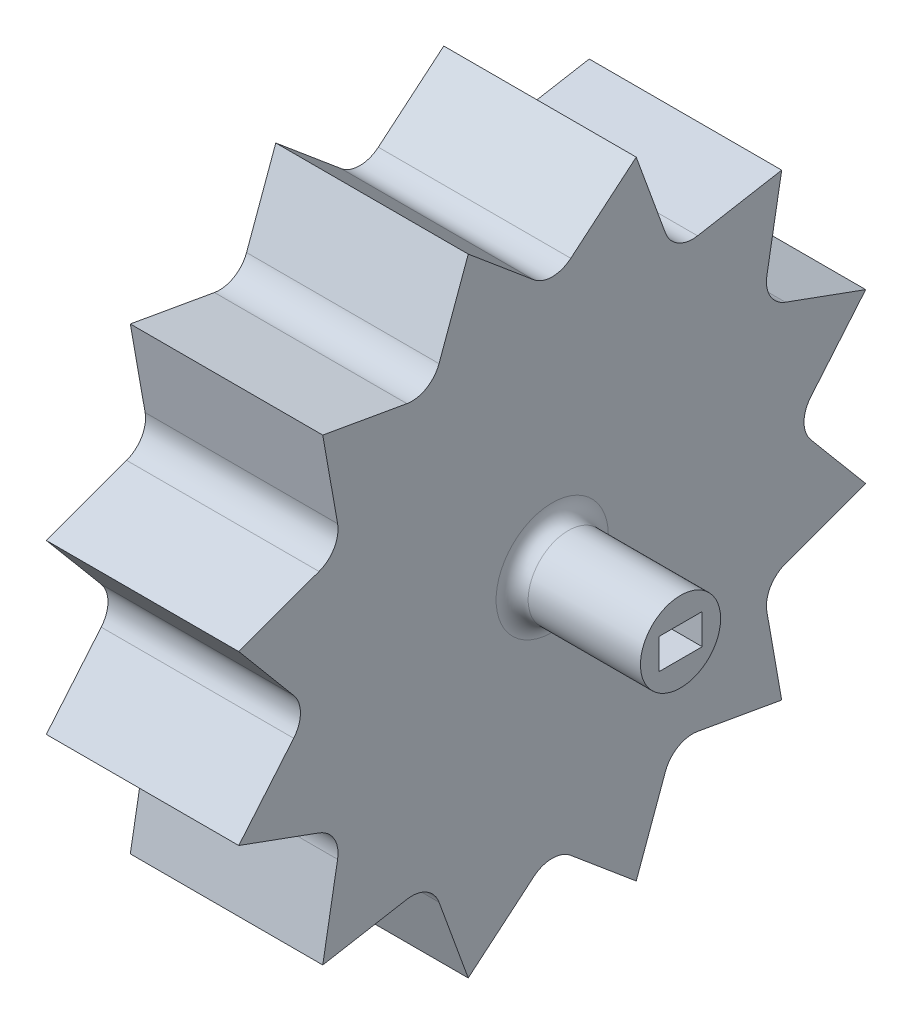
SolidWorks part; units mm, degrees
ref_plane "Front Plane" through (0, 0, 0) normal (0, 0, 1) x (1, 0, 0)
ref_plane "Top Plane" through (0, 0, 0) normal (0, 1, 0) x (1, 0, 0)
ref_plane "Right Plane" through (0, 0, 0) normal (1, 0, 0) x (0, 0, -1)
sketch "Sketch1" plane through (0, 0, 0) normal (1, 0, 0) x (0, 0, -1)
  line L0 (2.314, 32.2422) -> (10.4739, 39.0892)
  line L1 (10.4739, 39.0892) -> (14.1171, 29.0796)
  line L2 (18.1251, 26.7656) -> (28.6153, 28.6153)
  line L3 (28.6153, 28.6153) -> (26.7656, 18.1251)
  line L4 (29.0796, 14.1171) -> (39.0892, 10.4739)
  line L5 (39.0892, 10.4739) -> (32.2422, 2.314)
  line L6 (32.2422, -2.314) -> (39.0892, -10.4739)
  line L7 (39.0892, -10.4739) -> (29.0796, -14.1171)
  line L8 (26.7656, -18.1251) -> (28.6153, -28.6153)
  line L9 (28.6153, -28.6153) -> (18.1251, -26.7656)
  line L10 (14.1171, -29.0796) -> (10.4739, -39.0892)
  line L11 (10.4739, -39.0892) -> (2.314, -32.2422)
  line L12 (-2.314, -32.2422) -> (-10.4739, -39.0892)
  line L13 (-10.4739, -39.0892) -> (-14.1171, -29.0796)
  line L14 (-18.1251, -26.7656) -> (-28.6153, -28.6153)
  line L15 (-28.6153, -28.6153) -> (-26.7656, -18.1251)
  line L16 (-29.0796, -14.1171) -> (-39.0892, -10.4739)
  line L17 (-39.0892, -10.4739) -> (-32.2422, -2.314)
  line L18 (-32.2422, 2.314) -> (-39.0892, 10.4739)
  line L19 (-39.0892, 10.4739) -> (-29.0796, 14.1171)
  line L20 (-26.7656, 18.1251) -> (-28.6153, 28.6153)
  line L21 (-28.6153, 28.6153) -> (-18.1251, 26.7656)
  line L22 (-14.1171, 29.0796) -> (-10.4739, 39.0892)
  line L23 (-10.4739, 39.0892) -> (-2.314, 32.2422)
  line L24 (0, 0) -> (0, 112.2055) construction
  line L25 (0, 0) -> (10.4739, 39.0892) construction
  line L26 (-23.5324, 48.2012) -> (44.4802, 29.9772) construction
  line L27 (-11.5161, 39.3204) -> (47.9644, 23.3827) construction
  circle A0 centre (0, 0) radius 35 construction
  arc A1 (-2.314, 32.2422) -> (2.314, 32.2422) centre (0, 35) ccw
  arc A2 (14.1171, 29.0796) -> (18.1251, 26.7656) centre (17.5, 30.3109) ccw
  arc A3 (26.7656, 18.1251) -> (29.0796, 14.1171) centre (30.3109, 17.5) ccw
  arc A4 (32.2422, 2.314) -> (32.2422, -2.314) centre (35, 0) ccw
  arc A5 (29.0796, -14.1171) -> (26.7656, -18.1251) centre (30.3109, -17.5) ccw
  arc A6 (18.1251, -26.7656) -> (14.1171, -29.0796) centre (17.5, -30.3109) ccw
  arc A7 (2.314, -32.2422) -> (-2.314, -32.2422) centre (0, -35) ccw
  arc A8 (-14.1171, -29.0796) -> (-18.1251, -26.7656) centre (-17.5, -30.3109) ccw
  arc A9 (-26.7656, -18.1251) -> (-29.0796, -14.1171) centre (-30.3109, -17.5) ccw
  arc A10 (-32.2422, -2.314) -> (-32.2422, 2.314) centre (-35, 0) ccw
  arc A11 (-29.0796, 14.1171) -> (-26.7656, 18.1251) centre (-30.3109, 17.5) ccw
  arc A12 (-18.1251, 26.7656) -> (-14.1171, 29.0796) centre (-17.5, 30.3109) ccw
  point P16 (10.4739, 39.0892)
  point P65 (0, 0)
  dimension "D1" = 70
  dimension "D2" = 3.6
  dimension "D4" = 50
  dimension "D3" = 12
extrude "Boss-Extrude1" add sketch "Sketch1" along normal blind 24
sketch "Sketch2" plane through (24, 0, 0) normal (1, 0, 0) x (0, 0, -1)
  circle A0 centre (0, 0) radius 5
  dimension "D1" = 10
extrude "Boss-Extrude2" add sketch "Sketch2" along normal blind 16
fillet "Fillet1" radius 2 1 edges at (24, 0, -5)
sketch "Sketch4" plane through (40, 0, 0) normal (1, 0, 0) x (0, 0, -1)
  line L1 (-2.705, -1.9) -> (2.705, -1.9)
  line L2 (-2.705, -1.9) -> (-2.705, 1.9)
  line L3 (-2.705, 1.9) -> (2.705, 1.9)
  line L4 (2.705, -1.9) -> (2.705, 1.9)
  line L5 (-2.705, -1.9) -> (2.705, 1.9) construction
  line L6 (-2.705, 1.9) -> (2.705, -1.9) construction
  point P0 (0, 0)
  dimension "D1" = 5.41
  dimension "D2" = 3.8
extrude "Cut-Extrude1" cut sketch "Sketch4" against normal blind 20
